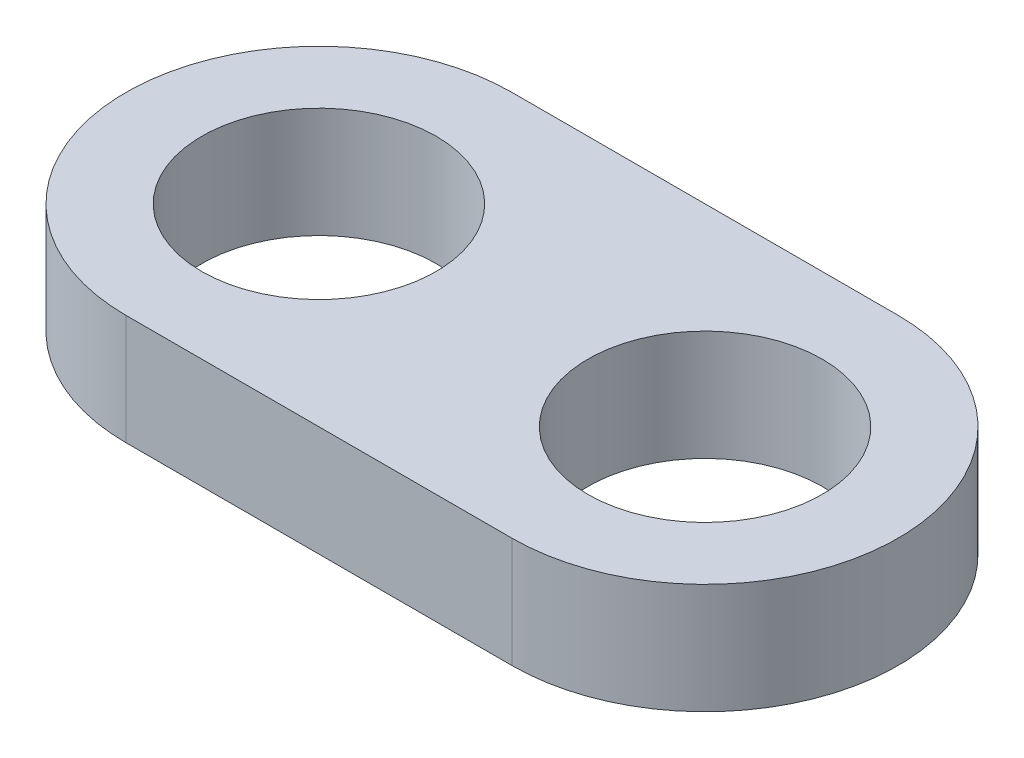
SolidWorks part; units mm, degrees
ref_plane "Front Plane" through (0, 0, 0) normal (0, 0, 1) x (1, 0, 0)
ref_plane "Top Plane" through (0, 0, 0) normal (0, 1, 0) x (1, 0, 0)
ref_plane "Right Plane" through (0, 0, 0) normal (1, 0, 0) x (0, 0, -1)
sketch "Sketch1" plane through (0, 0, 0) normal (0, 1, 0) x (1, 0, 0)
  line L0 (-3.5, 0) -> (3.5, 0) construction
  line L1 (-3.5, 3.5) -> (3.5, 3.5)
  line L2 (-3.5, -3.5) -> (3.5, -3.5)
  arc A0 (-3.5, 3.5) -> (-3.5, -3.5) centre (-3.5, 0) ccw
  arc A1 (3.5, -3.5) -> (3.5, 3.5) centre (3.5, 0) ccw
  circle A2 centre (-3.5, 0) radius 2.125
  circle A3 centre (3.5, 0) radius 2.125
  point P2 (0, 0)
  dimension "D3" = 4.25
  dimension "D1" = 7
  dimension "D2" = 7
extrude "Boss-Extrude1" add sketch "Sketch1" along normal mid plane 2
